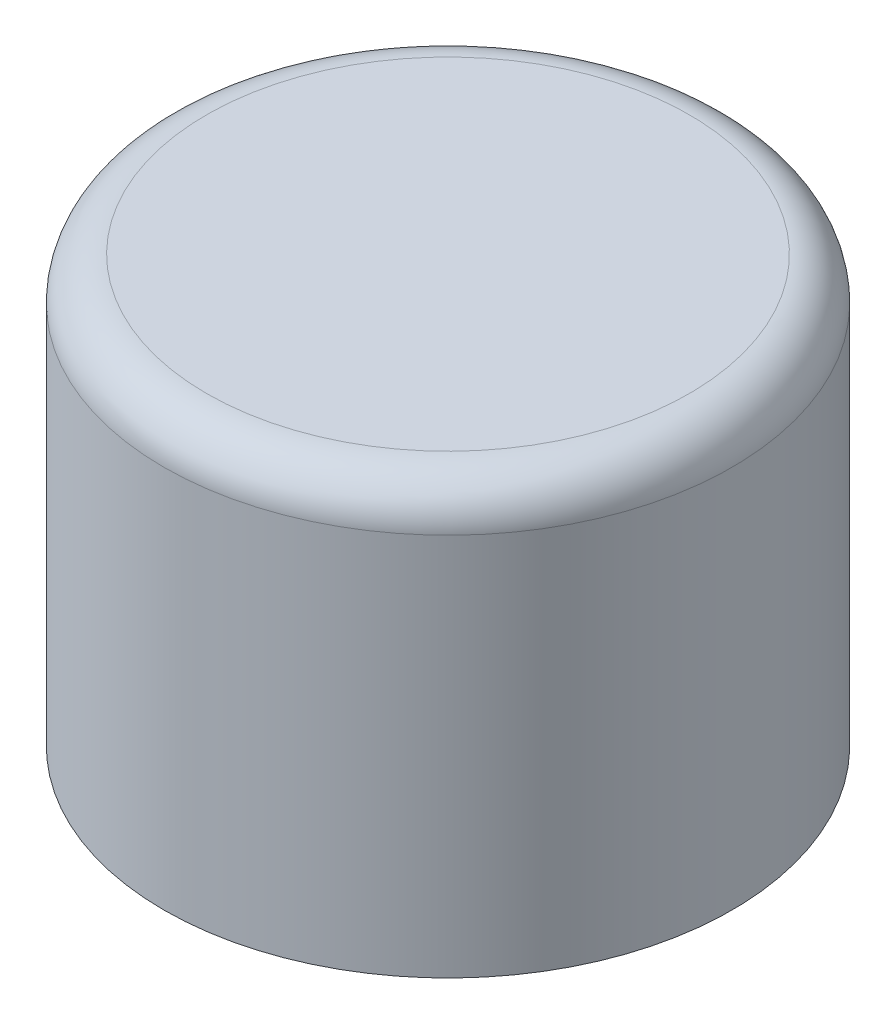
SolidWorks part; units mm, degrees
ref_plane "Plan de face" through (0, 0, 0) normal (0, 0, 1) x (1, 0, 0)
ref_plane "Plan de dessus" through (0, 0, 0) normal (0, 1, 0) x (1, 0, 0)
ref_plane "Plan de droite" through (0, 0, 0) normal (1, 0, 0) x (0, 0, -1)
sketch "Esquisse1" plane through (0, 0, 0) normal (0, 1, 0) x (1, 0, 0)
  circle A0 centre (0, 0) radius 2
extrude "Extrusion1" add sketch "Esquisse1" along normal blind 3
fillet "Congé1" radius 0.3 1 edges at (0, 3, 2)
